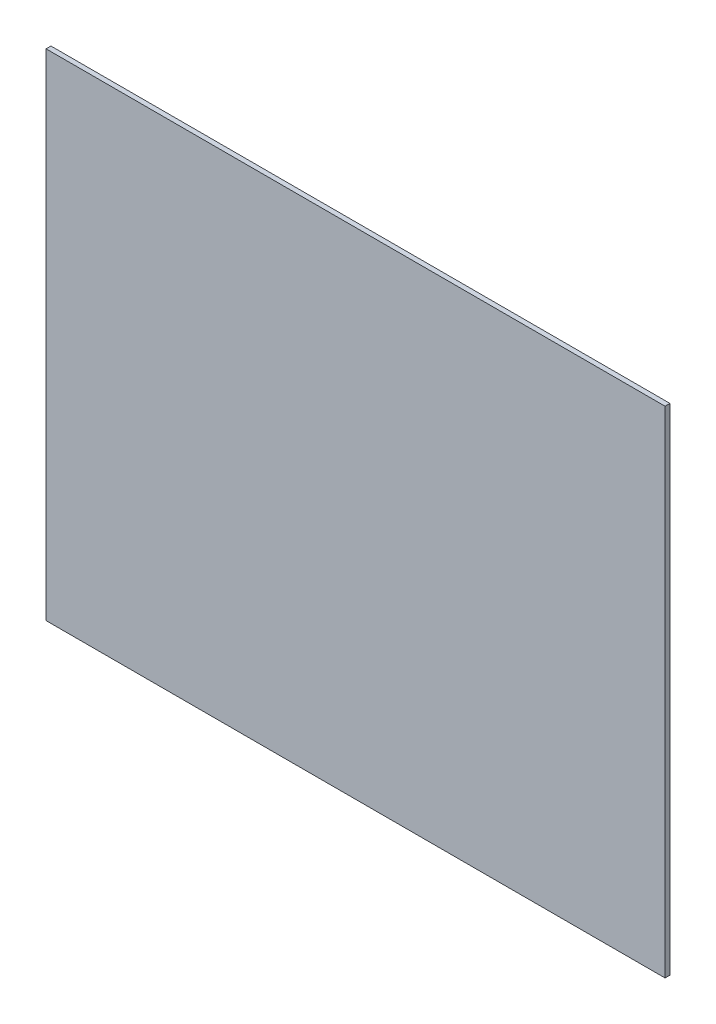
SolidWorks part; units mm, degrees
ref_plane "Front Plane" through (0, 0, 0) normal (0, 0, 1) x (1, 0, 0)
ref_plane "Top Plane" through (0, 0, 0) normal (0, 1, 0) x (1, 0, 0)
ref_plane "Right Plane" through (0, 0, 0) normal (1, 0, 0) x (0, 0, -1)
sketch "Sketch1" plane through (0, 0, 0) normal (0, 0, 1) x (1, 0, 0)
  line L1 (-95.25, 76.2) -> (95.25, 76.2)
  line L2 (-95.25, 76.2) -> (-95.25, -76.2)
  line L3 (-95.25, -76.2) -> (95.25, -76.2)
  line L4 (95.25, 76.2) -> (95.25, -76.2)
  line L5 (-95.25, 76.2) -> (95.25, -76.2) construction
  line L6 (-95.25, -76.2) -> (95.25, 76.2) construction
  point P0 (0, 0)
  dimension "D1" = 152.4
  dimension "D2" = 190.5
extrude "Boss-Extrude1" add sketch "Sketch1" along normal blind 1.5
